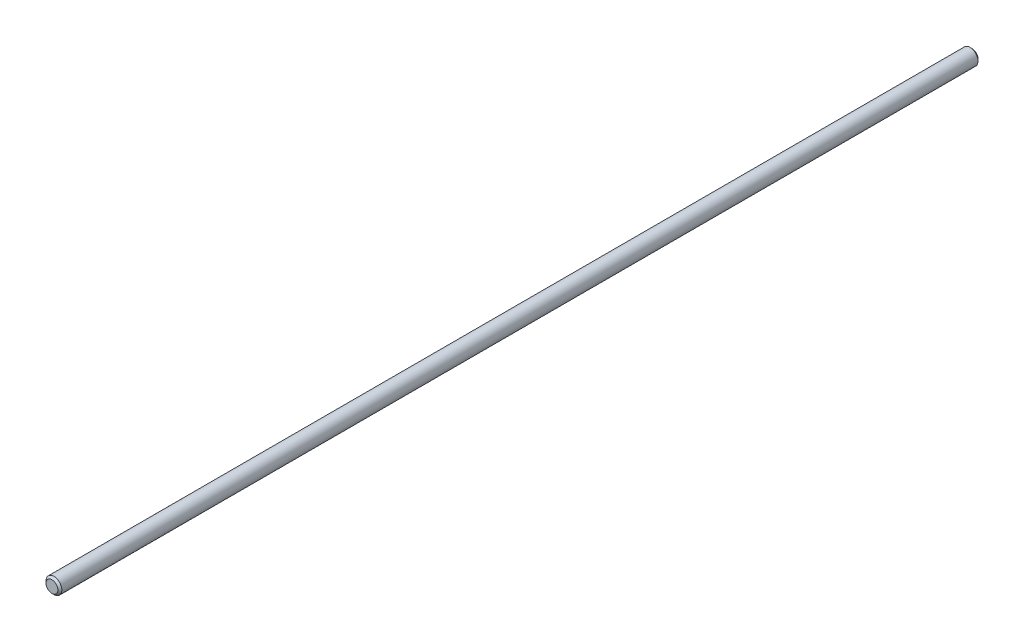
SolidWorks part; units mm, degrees
ref_plane "Piano frontale" through (0, 0, 0) normal (0, 0, 1) x (1, 0, 0)
ref_plane "Piano superiore" through (0, 0, 0) normal (0, 1, 0) x (1, 0, 0)
ref_plane "Piano destro" through (0, 0, 0) normal (1, 0, 0) x (0, 0, -1)
sketch "Schizzo1" plane through (0, 0, 0) normal (0, 0, 1) x (1, 0, 0)
  circle A0 centre (0, 0) radius 4
  dimension "D1" = 8
extrude "Estrusione-Estrusione1" add sketch "Schizzo1" along normal blind 465
chamfer "Smusso1" distance 1 angle 45 2 edges at (4, 0, 0) (4, 0, 465)
sketch "Schizzo2" plane through (0, 0, 0) normal (0, 1, 0) x (1, 0, 0)
  line L0 (4, -1) -> (4, -464) construction
